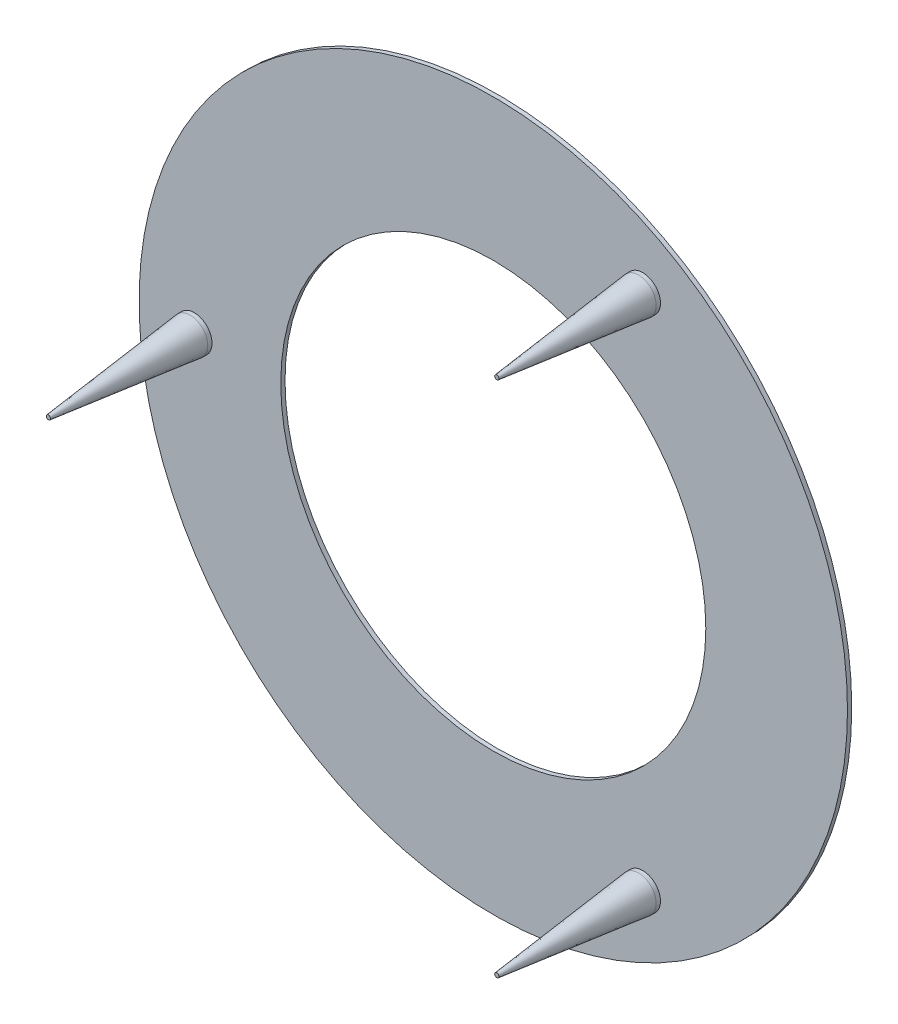
SolidWorks part; units mm, degrees
ref_plane "Front Plane" through (0, 0, 0) normal (0, 0, 1) x (1, 0, 0)
ref_plane "Top Plane" through (0, 0, 0) normal (0, 1, 0) x (1, 0, 0)
ref_plane "Right Plane" through (0, 0, 0) normal (1, 0, 0) x (0, 0, -1)
sketch "Sketch1" plane through (0, 0, 0) normal (0, 0, 1) x (1, 0, 0)
  circle A0 centre (0, 0) radius 63.5
  circle A1 centre (0, 0) radius 38.1
  dimension "D1" = 127
  dimension "D2" = 76.2
extrude "Boss-Extrude1" add sketch "Sketch1" along normal blind 0.762
sketch "Sketch2" plane through (0, 0, 0.762) normal (0, 0, 1) x (1, 0, 0)
  line L0 (-53.5973, 0) -> (0, 0) construction
  circle A0 centre (-53.5973, 0) radius 3.175
  dimension "D1" = 6.35
extrude "Boss-Extrude2" add sketch "Sketch2" along normal blind 26.162
chamfer "Chamfer1" distance 25.4 distance2 2.794 1 edges at (-50.4223, 0, 26.924)
pattern_circular "CirPattern3" count 3 over 360 about axis through (0, 0, 0) along (0, 0, 1) of "Chamfer1", "Boss-Extrude2"
